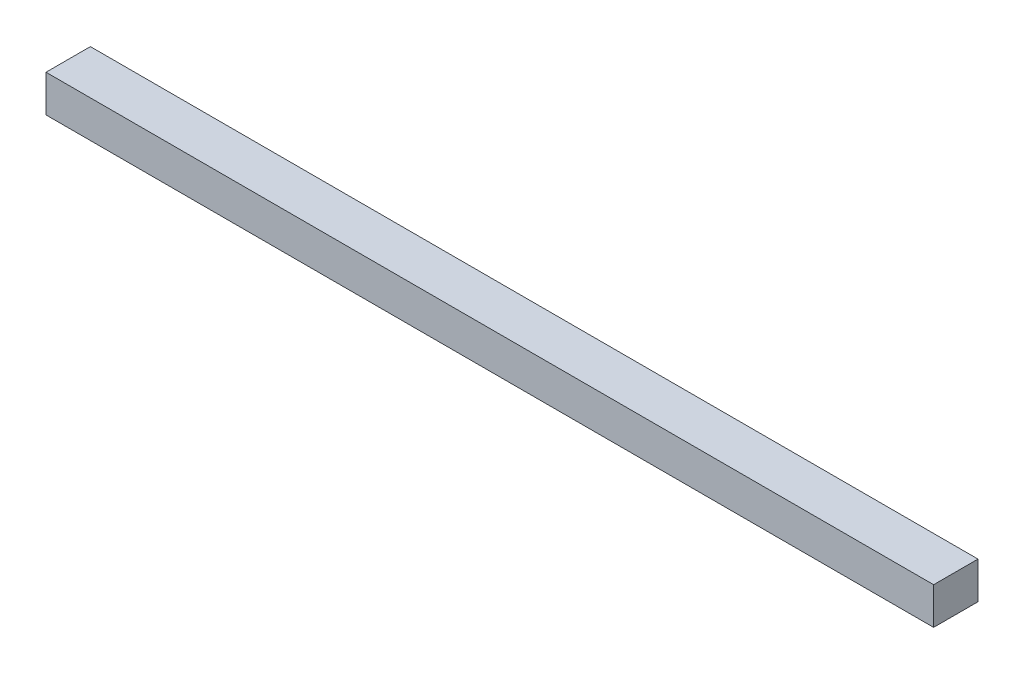
SolidWorks part; units mm, degrees
ref_plane "Спереди" through (0, 0, 0) normal (0, 0, 1) x (1, 0, 0)
ref_plane "Сверху" through (0, 0, 0) normal (0, 1, 0) x (1, 0, 0)
ref_plane "Справа" through (0, 0, 0) normal (1, 0, 0) x (0, 0, -1)
sketch "Эскиз2" plane through (0, 0, 0) normal (1, 0, 0) x (0, 0, -1)
  line L1 (-15, -12.5) -> (15, -12.5)
  line L2 (-15, -12.5) -> (-15, 12.5)
  line L3 (-15, 12.5) -> (15, 12.5)
  line L4 (15, -12.5) -> (15, 12.5)
  line L5 (-15, -12.5) -> (15, 12.5) construction
  line L6 (-15, 12.5) -> (15, -12.5) construction
  point P0 (0, 0)
extrude "Бобышка-Вытянуть1" add sketch "Эскиз2" along normal blind 600
